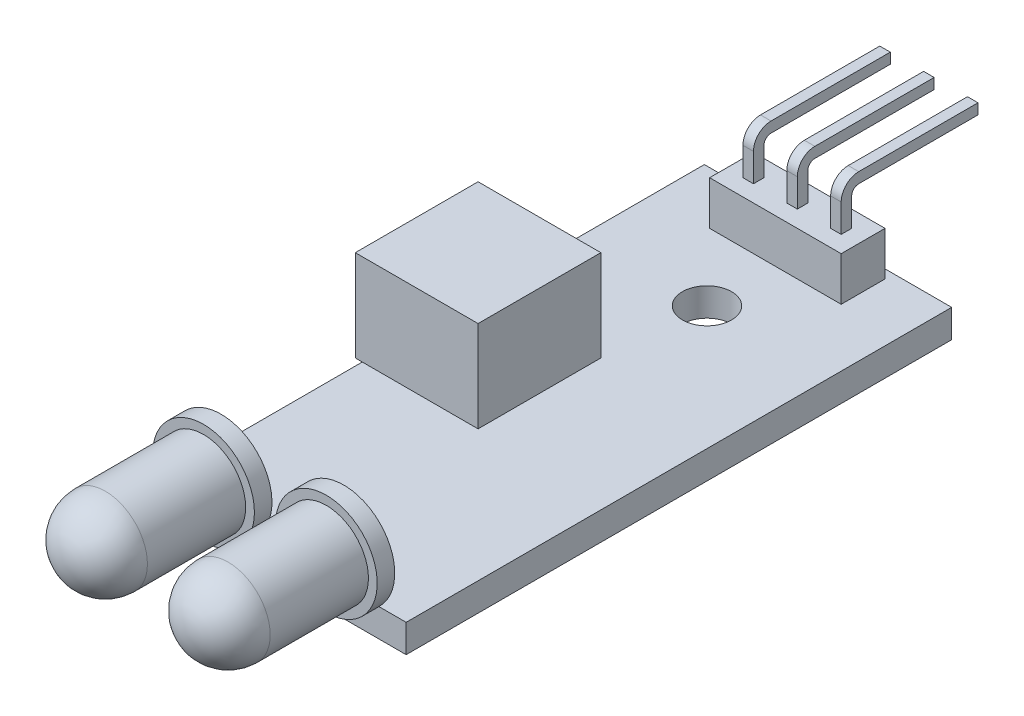
SolidWorks part; units mm, degrees
ref_plane "前视基准面" through (0, 0, 0) normal (0, 0, 1) x (1, 0, 0)
ref_plane "上视基准面" through (0, 0, 0) normal (0, 1, 0) x (1, 0, 0)
ref_plane "右视基准面" through (0, 0, 0) normal (1, 0, 0) x (0, 0, -1)
sketch "草图1" plane through (0, 0, 0) normal (0, 1, 0) x (1, 0, 0)
  line L1 (-7.05, -15.55) -> (7.05, -15.55)
  line L2 (-7.05, -15.55) -> (-7.05, 15.55)
  line L3 (-7.05, 15.55) -> (7.05, 15.55)
  line L4 (7.05, -15.55) -> (7.05, 15.55)
  line L5 (-7.05, -15.55) -> (7.05, 15.55) construction
  line L6 (-7.05, 15.55) -> (7.05, -15.55) construction
  circle A0 centre (0, 8.65) radius 1.4
  point P0 (0, 0)
  dimension "D3" = 2.8
  dimension "D1" = 14.1
  dimension "D2" = 31.1
  dimension "D4" = 6.9
extrude "凸台-拉伸1" add sketch "草图1" along normal blind 1.6
sketch "草图2" plane through (0, 0, 15.55) normal (0, 0, 1) x (1, 0, 0)
  line L0 (-7.05, 0) -> (7.05, 0) construction
  line L1 (0, 0) -> (0, 13.3253) construction
  circle A0 centre (-3.5, 3.7) radius 2.9
  dimension "D1" = 5.8
  dimension "D2" = 3.7
  dimension "D3" = 3.5
extrude "凸台-拉伸2" add sketch "草图2" along normal blind 1
sketch "草图3" plane through (0, 0, 16.55) normal (0, 0, 1) x (1, 0, 0)
  circle A0 centre (-3.5, 3.7) radius 2.4
  dimension "D1" = 4.8
extrude "凸台-拉伸3" add sketch "草图3" along normal blind 8
fillet "圆角1" radius 2.4 1 edges at (-1.1, 3.7, 24.55)
mirror "镜向1" about plane through (0, 0, 0) normal (1, 0, 0) of "圆角1", "凸台-拉伸3", "凸台-拉伸2"
sketch "草图4" plane through (0, 1.6, 0) normal (0, 1, 0) x (1, 0, 0)
  line L1 (-7.45, 3.05) -> (-0.45, 3.05)
  line L2 (-7.45, 3.05) -> (-7.45, -3.95)
  line L3 (-7.45, -3.95) -> (-0.45, -3.95)
  line L4 (-0.45, 3.05) -> (-0.45, -3.95)
  line L5 (-7.45, 3.05) -> (-0.45, -3.95) construction
  line L6 (-7.45, -3.95) -> (-0.45, 3.05) construction
  line L7 (-7.05, -15.55) -> (-5.5, -15.55) construction
  line L8 (7.05, -15.55) -> (7.05, 15.55) construction
  point P0 (-3.95, -0.45)
  point P5 (-6.275, -15.55)
  dimension "D1" = 7
  dimension "D2" = 7
  dimension "D3" = 11.6
  dimension "D4" = 7.5
extrude "凸台-拉伸4" add sketch "草图4" along normal blind 5.2
sketch "草图5" plane through (0, 1.6, 0) normal (0, 1, 0) x (1, 0, 0)
  line L0 (7.05, 15.55) -> (-7.05, 15.55) construction
  line L1 (1.25, 12.55) -> (-1.25, 12.55)
  line L2 (1.25, 12.55) -> (1.25, 15.05)
  line L3 (1.25, 15.05) -> (-1.25, 15.05)
  line L4 (-1.25, 12.55) -> (-1.25, 15.05)
  line L5 (1.25, 12.55) -> (-1.25, 15.05) construction
  line L6 (1.25, 15.05) -> (-1.25, 12.55) construction
  point P0 (0, 13.8)
  dimension "D1" = 2.5
  dimension "D2" = 0.5
extrude "凸台-拉伸5" add sketch "草图5" along normal blind 2.5
sketch "草图6" plane through (0, 0, 0) normal (1, 0, 0) x (0, 0, -1)
  line L0 (13.5, -0.5) -> (13.5, 5.7)
  line L1 (14.5, 6.7) -> (21.3, 6.7)
  line L2 (21.3, 6.7) -> (21.3, 6.1)
  line L3 (21.3, 6.1) -> (14.5, 6.1)
  line L4 (14.1, 5.7) -> (14.1, -0.5)
  line L5 (14.1, -0.5) -> (13.5, -0.5)
  line L6 (15.55, 0) -> (-15.55, 0) construction
  line L8 (15.05, 4.1) -> (15.05, 1.6) construction
  arc A0 (14.1, 5.7) -> (14.5, 6.1) centre (14.5, 5.7) cw
  arc A1 (13.5, 5.7) -> (14.5, 6.7) centre (14.5, 5.7) cw
  dimension "D4" = 0.4
  dimension "D5" = 1
  dimension "D1" = 0.5
  dimension "D2" = 0.6
  dimension "D3" = 0.6
  dimension "D6" = 6.7
  dimension "D7" = 7.8
  dimension "D8" = 0.95
extrude "凸台-拉伸6" add sketch "草图6" along normal mid plane 0.6
pattern_linear "阵列(线性)1" count 2 spacing 2.5 along (-1, 0, 0) count 2 spacing 2.5 along (1, 0, 0) of "凸台-拉伸5", "凸台-拉伸6"
